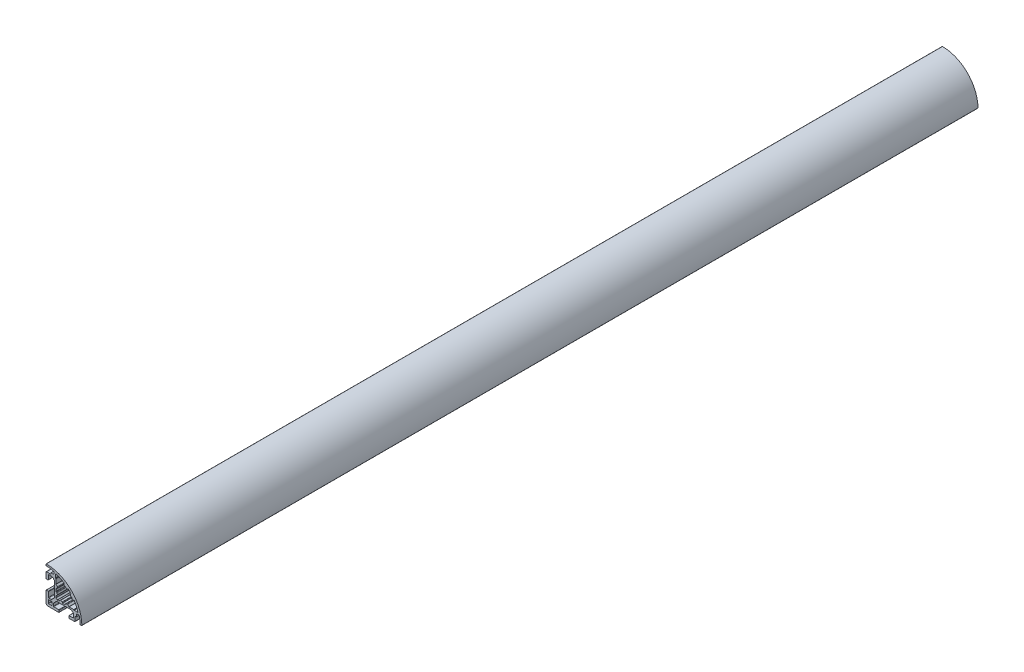
SolidWorks part; units mm, degrees
ref_plane "Plano frontal" through (0, 0, 0) normal (0, 0, 1) x (1, 0, 0)
ref_plane "Plano superior" through (0, 0, 0) normal (0, 1, 0) x (1, 0, 0)
ref_plane "Plano direito" through (0, 0, 0) normal (1, 0, 0) x (0, 0, -1)
ref_plane "Plano1" through (0, 0, 0) normal (0, 0, -1) x (-1, 0, 0)
sketch "Esboço1" plane through (0, 0, 0) normal (0, 0, -1) x (-1, 0, 0)
  line L0 (12.7, -13) -> (10.3, -13)
  line L1 (10, -12.7) -> (10, -10.3)
  line L2 (10.3, -10) -> (12.7, -10)
  line L3 (13, -10.3) -> (13, -12.7)
  line L4 (-0.95, 6.7) -> (-0.3, 6.7)
  line L5 (0, 7) -> (0, 8.4776)
  line L6 (7, 11.4273) -> (7, 8.6799)
  line L7 (6.9121, 8.4678) -> (6.7879, 8.3435)
  line L8 (6.7, 8.1314) -> (6.7, 4.3494)
  line L9 (6.6121, 4.1372) -> (5.4871, 3.0123)
  line L10 (6.1579, 1.25) -> (6.4, 1.25)
  line L11 (6.7, 0.95) -> (6.7, -0.95)
  line L12 (6.4, -1.25) -> (6.1579, -1.25)
  line L13 (5.4871, -3.0123) -> (6.6121, -4.1372)
  line L14 (6.7, -4.3494) -> (6.7, -5.4396)
  line L15 (6.6121, -5.6517) -> (5.6517, -6.6121)
  line L16 (5.4395, -6.7) -> (4.3494, -6.7)
  line L17 (4.1373, -6.6121) -> (3.0123, -5.4871)
  line L18 (1.25, -6.1579) -> (1.25, -6.4)
  line L19 (0.95, -6.7) -> (-0.95, -6.7)
  line L20 (-1.25, -6.4) -> (-1.25, -6.1579)
  line L21 (-3.0123, -5.4871) -> (-4.1373, -6.6121)
  line L22 (-4.3494, -6.7) -> (-8.1314, -6.7)
  line L23 (-8.3435, -6.7879) -> (-8.4678, -6.9121)
  line L24 (-8.6799, -7) -> (-11.4273, -7)
  line L25 (-8.4777, 0) -> (-7, 0)
  line L26 (-6.7, 0.3) -> (-6.7, 0.95)
  line L27 (-6.4, 1.25) -> (-6.1579, 1.25)
  line L28 (-5.4871, 3.0123) -> (-5.7974, 3.3226)
  line L29 (-3.3226, 5.7974) -> (-3.0123, 5.4871)
  line L30 (-1.25, 6.1579) -> (-1.25, 6.4)
  line L31 (7.9882, 6.432) -> (8.7045, 7.072)
  line L32 (8.7045, 7.072) -> (8.7283, 7.4958)
  line L33 (8.7283, 7.4958) -> (9.1516, 7.472)
  line L34 (9.1516, 7.472) -> (9.8678, 8.112)
  line L35 (10.08, 8.1999) -> (12.7001, 8.1998)
  line L36 (13.0001, 7.8998) -> (13, 4.3499)
  line L37 (13.3, 4.0499) -> (14.7, 4.0498)
  line L38 (15, 4.3498) -> (15, 8.8999)
  line L39 (14.5, 9.3999) -> (11.3, 9.3999)
  line L40 (11, 9.6999) -> (11, 10.1999)
  line L41 (10.7, 10.4999) -> (8.8, 10.4999)
  line L42 (8.5, 10.7999) -> (8.5, 12.51)
  line L43 (15, 13.7984) -> (15, 14.6985)
  line L44 (-14.6985, -15) -> (-13.7984, -15)
  line L45 (-12.5105, -8.5) -> (-10.8005, -8.5)
  line L46 (-10.5005, -8.8) -> (-10.5005, -10.7)
  line L47 (-10.2005, -11) -> (-9.7004, -11)
  line L48 (-9.4004, -11.3) -> (-9.4004, -14.5)
  line L49 (-8.9004, -15) -> (-4.3504, -15)
  line L50 (-4.0504, -14.7) -> (-4.0504, -13.3)
  line L51 (-4.3504, -13) -> (-7.9004, -12.9999)
  line L52 (-8.2004, -12.6999) -> (-8.2004, -10.0799)
  line L53 (-8.1125, -9.8677) -> (-7.4725, -9.1515)
  line L54 (-7.4725, -9.1515) -> (-7.4963, -8.728)
  line L55 (-7.4963, -8.728) -> (-7.0727, -8.7042)
  line L56 (-7.0727, -8.7042) -> (-6.4326, -7.988)
  line L57 (-6.2205, -7.9001) -> (6.2197, -7.9001)
  line L58 (6.4318, -7.988) -> (8.7117, -10.4679)
  line L59 (8.7996, -10.6801) -> (8.7996, -12.7001)
  line L60 (8.4996, -13.0001) -> (4.3496, -13.0001)
  line L61 (4.0496, -13.3001) -> (4.0496, -14.7)
  line L62 (4.3496, -15) -> (13.5, -15)
  line L63 (15, -13.5) -> (15, -4.3503)
  line L64 (14.7, -4.0503) -> (13.2999, -4.0503)
  line L65 (12.9999, -4.3503) -> (12.9999, -8.5003)
  line L66 (12.6999, -8.8003) -> (10.6798, -8.8003)
  line L67 (10.4677, -8.7124) -> (7.9878, -6.4325)
  line L68 (7.9003, -6.2203) -> (7.9003, 6.2198)
  arc A0 (10.3, -13) -> (10, -12.7) centre (10.3, -12.7) cw
  arc A1 (10, -10.3) -> (10.3, -10) centre (10.3, -10.3) cw
  arc A2 (12.7, -10) -> (13, -10.3) centre (12.7, -10.3) cw
  arc A3 (13, -12.7) -> (12.7, -13) centre (12.7, -12.7) cw
  arc A4 (-0.3, 6.7) -> (0, 7) centre (-0.3, 7) ccw
  arc A5 (0, 8.4776) -> (0.1408, 8.7319) centre (0.3, 8.4776) cw
  arc A6 (0.1408, 8.7319) -> (6.6101, 11.7135) centre (15, -15) cw
  arc A7 (6.6101, 11.7135) -> (7, 11.4273) centre (6.7, 11.4273) cw
  arc A8 (7, 8.6799) -> (6.9121, 8.4678) centre (6.7, 8.6799) cw
  arc A9 (6.7879, 8.3435) -> (6.7, 8.1314) centre (7, 8.1314) ccw
  arc A10 (6.7, 4.3494) -> (6.6121, 4.1372) centre (6.4, 4.3494) cw
  arc A11 (5.4871, 3.0123) -> (5.43, 2.6678) centre (5.6993, 2.8001) ccw
  arc A12 (5.43, 2.6678) -> (5.867, 1.4768) centre (0, 0) cw
  arc A13 (5.867, 1.4768) -> (6.1579, 1.25) centre (6.1579, 1.55) ccw
  arc A14 (6.4, 1.25) -> (6.7, 0.95) centre (6.4, 0.95) cw
  arc A15 (6.7, -0.95) -> (6.4, -1.25) centre (6.4, -0.95) cw
  arc A16 (6.1579, -1.25) -> (5.867, -1.4768) centre (6.1579, -1.55) ccw
  arc A17 (5.867, -1.4768) -> (5.43, -2.6678) centre (0, 0) cw
  arc A18 (5.43, -2.6678) -> (5.4871, -3.0123) centre (5.6993, -2.8001) ccw
  arc A19 (6.6121, -4.1372) -> (6.7, -4.3494) centre (6.4, -4.3494) cw
  arc A20 (6.7, -5.4396) -> (6.6121, -5.6517) centre (6.4, -5.4396) cw
  arc A21 (5.6517, -6.6121) -> (5.4395, -6.7) centre (5.4395, -6.4) cw
  arc A22 (4.3494, -6.7) -> (4.1373, -6.6121) centre (4.3494, -6.4) cw
  arc A23 (3.0123, -5.4871) -> (2.6678, -5.43) centre (2.8001, -5.6993) ccw
  arc A24 (2.6678, -5.43) -> (1.4768, -5.867) centre (0, 0) cw
  arc A25 (1.4768, -5.867) -> (1.25, -6.1579) centre (1.55, -6.1579) ccw
  arc A26 (1.25, -6.4) -> (0.95, -6.7) centre (0.95, -6.4) cw
  arc A27 (-0.95, -6.7) -> (-1.25, -6.4) centre (-0.95, -6.4) cw
  arc A28 (-1.25, -6.1579) -> (-1.4768, -5.867) centre (-1.55, -6.1579) ccw
  arc A29 (-1.4768, -5.867) -> (-2.6678, -5.43) centre (0, 0) cw
  arc A30 (-2.6678, -5.43) -> (-3.0123, -5.4871) centre (-2.8001, -5.6993) ccw
  arc A31 (-4.1373, -6.6121) -> (-4.3494, -6.7) centre (-4.3494, -6.4) cw
  arc A32 (-8.1314, -6.7) -> (-8.3435, -6.7879) centre (-8.1314, -7) ccw
  arc A33 (-8.4678, -6.9121) -> (-8.6799, -7) centre (-8.6799, -6.7) cw
  arc A34 (-11.4273, -7) -> (-11.7135, -6.6101) centre (-11.4273, -6.7) cw
  arc A35 (-11.7135, -6.6101) -> (-8.7319, -0.1408) centre (15, -15) cw
  arc A36 (-8.7319, -0.1408) -> (-8.4777, 0) centre (-8.4777, -0.3) cw
  arc A37 (-7, 0) -> (-6.7, 0.3) centre (-7, 0.3) ccw
  arc A38 (-6.7, 0.95) -> (-6.4, 1.25) centre (-6.4, 0.95) cw
  arc A39 (-6.1579, 1.25) -> (-5.867, 1.4768) centre (-6.1579, 1.55) ccw
  arc A40 (-5.867, 1.4768) -> (-5.43, 2.6678) centre (0, 0) cw
  arc A41 (-5.43, 2.6678) -> (-5.4871, 3.0123) centre (-5.6993, 2.8001) ccw
  arc A42 (-5.7974, 3.3226) -> (-5.8083, 3.7354) centre (-5.5853, 3.5347) cw
  arc A43 (-5.8083, 3.7354) -> (-3.7354, 5.8083) centre (15, -15) cw
  arc A44 (-3.7354, 5.8083) -> (-3.3226, 5.7974) centre (-3.5347, 5.5853) cw
  arc A45 (-3.0123, 5.4871) -> (-2.6678, 5.43) centre (-2.8001, 5.6993) ccw
  arc A46 (-2.6678, 5.43) -> (-1.4768, 5.867) centre (0, 0) cw
  arc A47 (-1.4768, 5.867) -> (-1.25, 6.1579) centre (-1.55, 6.1579) ccw
  arc A48 (-1.25, 6.4) -> (-0.95, 6.7) centre (-0.95, 6.4) cw
  arc A49 (9.8678, 8.112) -> (10.08, 8.1999) centre (10.08, 7.8999) cw
  arc A50 (12.7001, 8.1998) -> (13.0001, 7.8998) centre (12.7001, 7.8998) cw
  arc A51 (13, 4.3499) -> (13.3, 4.0499) centre (13.3, 4.3499) ccw
  arc A52 (14.7, 4.0498) -> (15, 4.3498) centre (14.7, 4.3498) ccw
  arc A53 (15, 8.8999) -> (14.5, 9.3999) centre (14.5, 8.8999) ccw
  arc A54 (11.3, 9.3999) -> (11, 9.6999) centre (11.3, 9.6999) cw
  arc A55 (11, 10.1999) -> (10.7, 10.4999) centre (10.7, 10.1999) ccw
  arc A56 (8.8, 10.4999) -> (8.5, 10.7999) centre (8.8, 10.7999) cw
  arc A57 (8.5, 12.51) -> (8.734, 12.8026) centre (8.8, 12.51) cw
  arc A58 (8.734, 12.8026) -> (14.7031, 13.4984) centre (15, -15) cw
  arc A59 (14.7031, 13.4984) -> (15, 13.7984) centre (14.7, 13.7984) ccw
  arc A60 (15, 14.6985) -> (14.697, 14.9985) centre (14.7, 14.6985) ccw
  arc A61 (14.697, 14.9985) -> (-14.9985, -14.697) centre (15, -15) ccw
  arc A62 (-14.9985, -14.697) -> (-14.6985, -15) centre (-14.6985, -14.7) ccw
  arc A63 (-13.7984, -15) -> (-13.4985, -14.7031) centre (-13.7984, -14.7) ccw
  arc A64 (-13.4985, -14.7031) -> (-12.8027, -8.734) centre (15, -15) cw
  arc A65 (-12.8027, -8.734) -> (-12.5105, -8.5) centre (-12.51, -8.8) cw
  arc A66 (-10.8005, -8.5) -> (-10.5005, -8.8) centre (-10.8005, -8.8) cw
  arc A67 (-10.5005, -10.7) -> (-10.2005, -11) centre (-10.2005, -10.7) ccw
  arc A68 (-9.7004, -11) -> (-9.4004, -11.3) centre (-9.7004, -11.3) cw
  arc A69 (-9.4004, -14.5) -> (-8.9004, -15) centre (-8.9004, -14.5) ccw
  arc A70 (-4.3504, -15) -> (-4.0504, -14.7) centre (-4.3504, -14.7) ccw
  arc A71 (-4.0504, -13.3) -> (-4.3504, -13) centre (-4.3504, -13.3) ccw
  arc A72 (-7.9004, -12.9999) -> (-8.2004, -12.6999) centre (-7.9004, -12.6999) cw
  arc A73 (-8.2004, -10.0799) -> (-8.1125, -9.8677) centre (-7.9004, -10.0799) cw
  arc A74 (-6.4326, -7.988) -> (-6.2205, -7.9001) centre (-6.2205, -8.2001) cw
  arc A75 (6.2197, -7.9001) -> (6.4318, -7.988) centre (6.2197, -8.2001) cw
  arc A76 (8.7117, -10.4679) -> (8.7996, -10.6801) centre (8.4996, -10.6801) cw
  arc A77 (8.7996, -12.7001) -> (8.4996, -13.0001) centre (8.4996, -12.7001) cw
  arc A78 (4.3496, -13.0001) -> (4.0496, -13.3001) centre (4.3496, -13.3001) ccw
  arc A79 (4.0496, -14.7) -> (4.3496, -15) centre (4.3496, -14.7) ccw
  arc A80 (13.5, -15) -> (15, -13.5) centre (13.5, -13.5) ccw
  arc A81 (15, -4.3503) -> (14.7, -4.0503) centre (14.7, -4.3503) ccw
  arc A82 (13.2999, -4.0503) -> (12.9999, -4.3503) centre (13.2999, -4.3503) ccw
  arc A83 (12.9999, -8.5003) -> (12.6999, -8.8003) centre (12.6999, -8.5003) cw
  arc A84 (10.6798, -8.8003) -> (10.4677, -8.7124) centre (10.6798, -8.5003) cw
  arc A85 (7.9878, -6.4325) -> (7.9003, -6.2203) centre (8.2003, -6.2208) cw
  arc A86 (7.9003, 6.2198) -> (7.9882, 6.432) centre (8.2003, 6.2198) cw
  dimension "D1" = 1.5
  dimension "D2" = 30
extrude "Ressalto-extrusão1" add sketch "Esboço1" against normal blind 750
sketch "Esboço3" plane through (0, 0, 0) normal (0, 0, -1) x (-1, 0, 0)
  line L0 (15, -13.5) -> (15, -4.3503) construction
  line L1 (-15, -15) -> (15, -15) construction
  line L2 (-15, -15) -> (-15, 15) construction
  line L3 (-15, 15) -> (15, 15) construction
  line L4 (15, -15) -> (15, 15) construction
  line L5 (-15, -15) -> (15, 15) construction
  line L6 (-15, 15) -> (15, -15) construction
  line L7 (-8.9004, -15) -> (-4.3504, -15) construction
  point P0 (0, 0)
  dimension "D1" = 30
  dimension "D2" = 30
